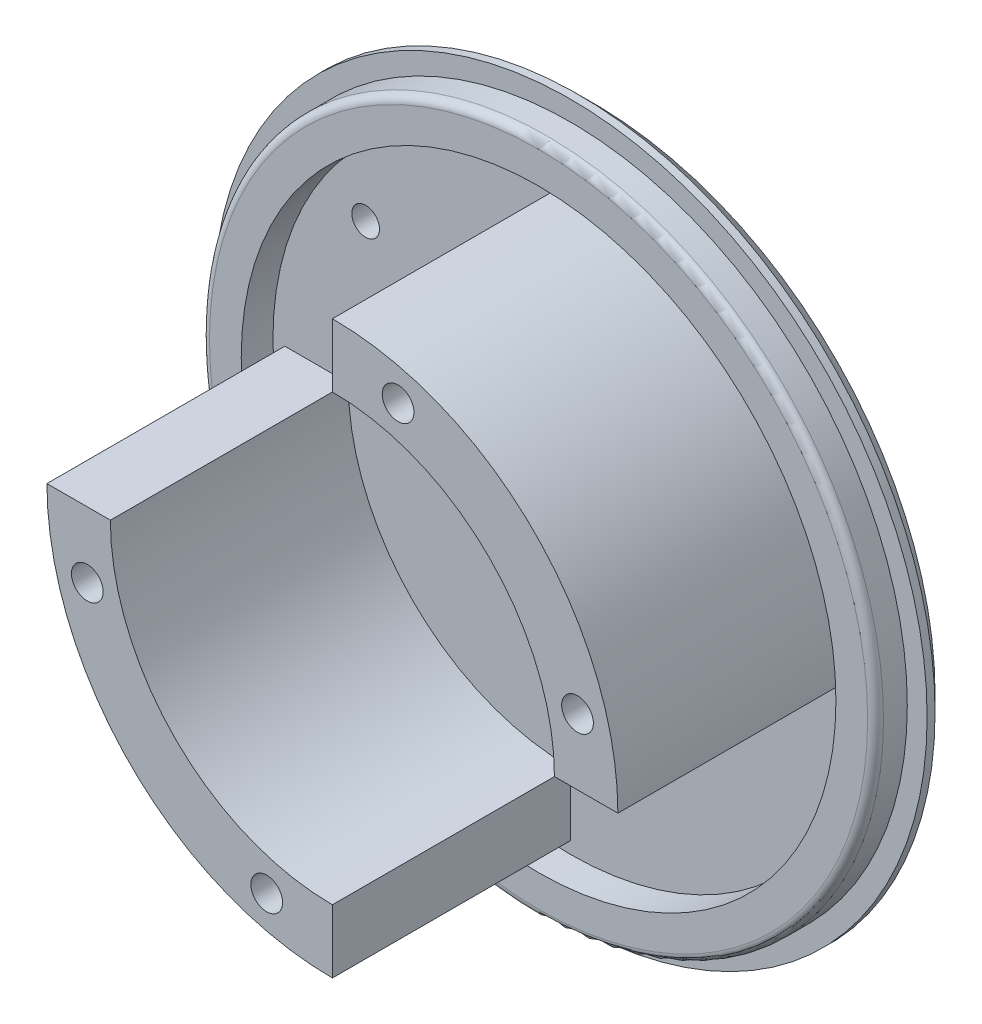
SolidWorks part; units mm, degrees
ref_plane "Front Plane" through (0, 0, 0) normal (0, 0, 1) x (1, 0, 0)
ref_plane "Top Plane" through (0, 0, 0) normal (0, 1, 0) x (1, 0, 0)
ref_plane "Right Plane" through (0, 0, 0) normal (1, 0, 0) x (0, 0, -1)
sketch "Sketch1" plane through (0, 0, 0) normal (0, 0, 1) x (1, 0, 0)
  circle A0 centre (0, 0) radius 45
  dimension "D1" = 90
extrude "Boss-Extrude1" add sketch "Sketch1" along normal blind 3
sketch "Sketch2" plane through (0, 0, 3) normal (0, 0, 1) x (1, 0, 0)
  circle A0 centre (0, 0) radius 42.5
  circle A1 centre (0, 0) radius 37.5
  dimension "D1" = 85
  dimension "D2" = 5
extrude "Boss-Extrude2" add sketch "Sketch2" along normal blind 4
chamfer "Chamfer1" distance 2 angle 45 1 edges at (45, 0, 0)
fillet "Fillet1" radius 1 1 edges at (42.5, 0, 7)
sketch "Sketch3" plane through (0, 0, 3) normal (0, 0, 1) x (1, 0, 0)
  line L0 (-36, 0) -> (-28, 0)
  line L1 (0, -28) -> (0, -36)
  arc A0 (-36, 0) -> (0, -36) centre (0, 0) ccw
  arc A2 (-28, 0) -> (0, -28) centre (0, 0) ccw
  circle A3 centre (0, 0) radius 28 construction
  circle A4 centre (0, 0) radius 36 construction
  dimension "D1" = 72
  dimension "D2" = 8
extrude "Boss-Extrude3" add sketch "Sketch3" along normal blind 30
sketch "Sketch4" plane through (0, 0, 33) normal (0, 0, 1) x (1, 0, 0)
  line L0 (-32, 0) -> (0, 0) construction
  line L1 (0, 0) -> (0, -32) construction
  line L2 (-30.9096, -8.2822) -> (0, 0) construction
  line L3 (0, 0) -> (-8.2822, -30.9096) construction
  circle A1 centre (-30.9096, -8.2822) radius 2
  arc A2 (-32, 0) -> (0, -32) centre (0, 0) ccw
  arc A3 (-32, 0) -> (0, -32) centre (0, 0) ccw construction
  circle A4 centre (-8.2822, -30.9096) radius 2
  dimension "D4" = 4
  dimension "D2" = 15
  dimension "D3" = 15
  dimension "D1" = 4
extrude "Cut-Extrude1" cut sketch "Sketch4" against normal blind 15
pattern_circular "CirPattern1" count 2 every 180 about axis through (0, 0, 0) along (0, 0, 1) of "Boss-Extrude3", "Cut-Extrude1"
sketch "Sketch5" plane through (0, 0, 3) normal (0, 0, 1) x (1, 0, 0)
  line L0 (0, 0) -> (-16.2635, 16.2635) construction
  line L1 (-16.2635, 16.2635) -> (-19.799, 12.7279) construction
  line L2 (-25.8094, 18.7383) -> (-13.7886, 6.7175) construction
  line L3 (0, 0) -> (0, 28) construction
  arc A0 (28, 0) -> (0, 28) centre (0, 0) ccw construction
  arc A1 (28, 0) -> (0, 28) centre (0, 0) ccw construction
  circle A2 centre (-25.8094, 18.7383) radius 1.75
  circle A3 centre (-13.7886, 6.7175) radius 1.75
  dimension "D5" = 3.5
  dimension "D1" = 45
  dimension "D2" = 5
  dimension "D3" = 17
  dimension "D4" = 23
extrude "Cut-Extrude2" cut sketch "Sketch5" against normal through all
